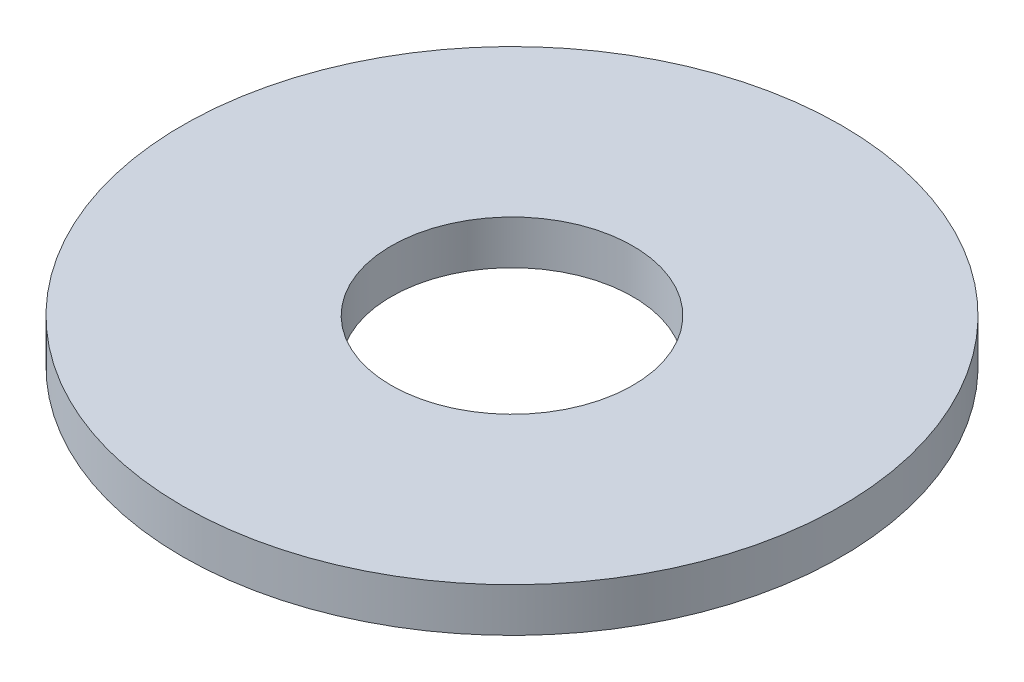
SolidWorks part; units mm, degrees
ref_plane "Plan de face" through (0, 0, 0) normal (0, 0, 1) x (1, 0, 0)
ref_plane "Plan de dessus" through (0, 0, 0) normal (0, 1, 0) x (1, 0, 0)
ref_plane "Plan de droite" through (0, 0, 0) normal (1, 0, 0) x (0, 0, -1)
sketch "Esquisse1" plane through (0, 0, 0) normal (0, 1, 0) x (1, 0, 0)
  circle A0 centre (0, 0) radius 2.75
  circle A1 centre (0, 0) radius 7.5
  dimension "D1" = 5.5
  dimension "D2" = 15
extrude "Extrusion1" add sketch "Esquisse1" along normal blind 1
